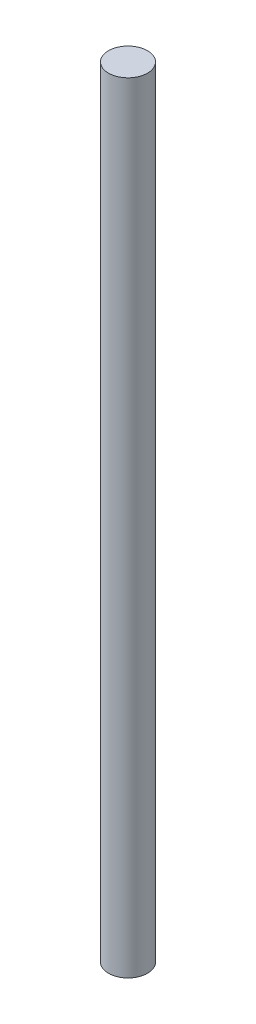
SolidWorks part; units mm, degrees
ref_plane "Front Plane" through (0, 0, 0) normal (0, 0, 1) x (1, 0, 0)
ref_plane "Top Plane" through (0, 0, 0) normal (0, 1, 0) x (1, 0, 0)
ref_plane "Right Plane" through (0, 0, 0) normal (1, 0, 0) x (0, 0, -1)
sketch "Sketch1" plane through (0, 0, 0) normal (0, 1, 0) x (1, 0, 0)
  circle A0 centre (0, 0) radius 12.7
  dimension "D1" = 25.4
extrude "Extrude1" add sketch "Sketch1" along normal blind 508
